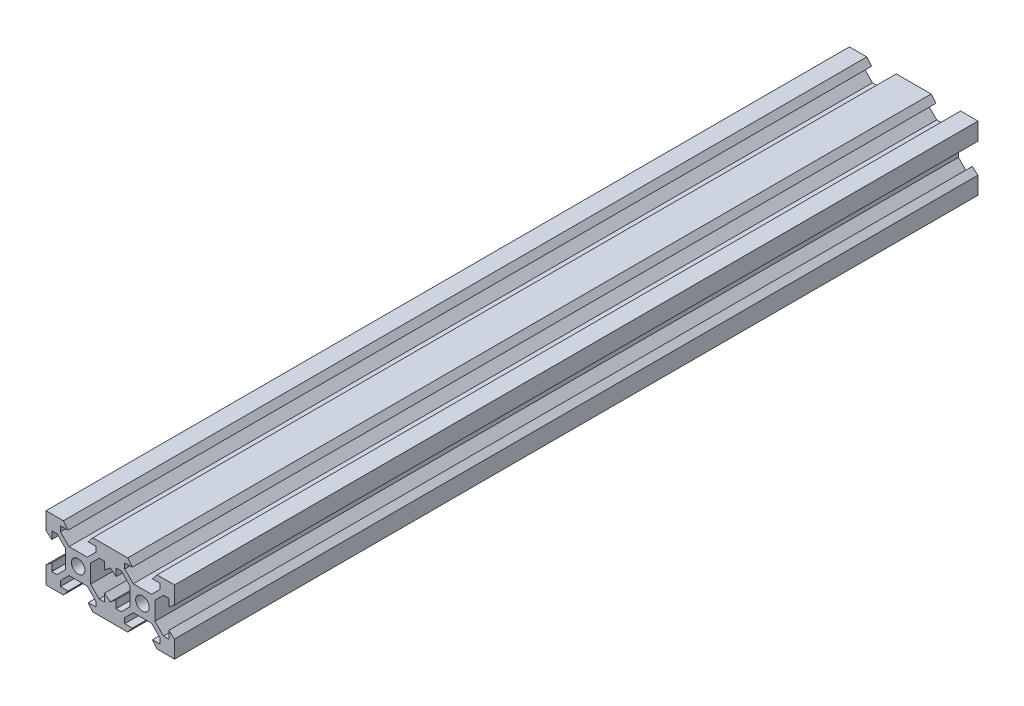
SolidWorks part; units mm, degrees
ref_plane "Front Plane" through (0, 0, 0) normal (0, 0, 1) x (1, 0, 0)
ref_plane "Top Plane" through (0, 0, 0) normal (0, 1, 0) x (1, 0, 0)
ref_plane "Right Plane" through (0, 0, 0) normal (1, 0, 0) x (0, 0, -1)
sketch "Sketch2" plane through (0, 0, 0) normal (0, 0, 1) x (1, 0, 0)
  line L0 (-5.5, 8.2) -> (-5.5, 6.5607)
  line L3 (-10, 10) -> (-4.58, 10)
  line L6 (-10, 10) -> (0, 0)
  line L9 (0, 0) -> (0, 10) construction
  line L16 (-2.8393, 3.9) -> (0, 3.9)
  line L20 (-5.5, 6.5607) -> (-2.8393, 3.9)
  line L21 (-5.5, 8.2) -> (-3.125, 8.2)
  line L22 (-3.125, 8.2) -> (-4.58, 10)
  line L23 (-4.58, 10) -> (-10, 10)
  line L24 (-2.8393, 3.9) -> (0, 3.9)
  line L25 (0, 3.9) -> (0, 2.1)
  line L26 (-3.9, 0) -> (-2.1, 0)
  line L27 (-3.125, 8.2) -> (-5.5, 8.2)
  line L28 (-4.58, 10) -> (-10, 10)
  line L29 (-3.125, 8.2) -> (-5.5, 8.2)
  line L30 (-3.9, 2.8393) -> (-3.9, 0)
  line L32 (-6.5607, 5.5) -> (-3.9, 2.8393)
  line L33 (-8.2, 5.5) -> (-6.5607, 5.5)
  line L34 (-8.2, 5.5) -> (-8.2, 3.125)
  line L35 (-8.2, 3.125) -> (-10, 4.58)
  line L36 (-10, 10) -> (-10, 4.58)
  line L37 (10, 10) -> (10, 4.58)
  line L38 (10, 10) -> (4.58, 10)
  line L39 (3.125, 8.2) -> (4.58, 10)
  line L40 (5.5, 8.2) -> (3.125, 8.2)
  line L41 (5.5, 8.2) -> (5.5, 6.5607)
  line L42 (5.5, 6.5607) -> (2.8393, 3.9)
  line L43 (2.8393, 3.9) -> (0, 3.9)
  line L44 (3.9, 2.8393) -> (3.9, 0)
  line L45 (6.5607, 5.5) -> (3.9, 2.8393)
  line L46 (8.2, 5.5) -> (6.5607, 5.5)
  line L47 (8.2, 5.5) -> (8.2, 3.125)
  line L48 (8.2, 3.125) -> (10, 4.58)
  line L49 (10, -10) -> (4.58, -10)
  line L50 (10, -10) -> (10, -4.58)
  line L51 (8.2, -3.125) -> (10, -4.58)
  line L52 (8.2, -5.5) -> (8.2, -3.125)
  line L53 (8.2, -5.5) -> (6.5607, -5.5)
  line L54 (6.5607, -5.5) -> (3.9, -2.8393)
  line L55 (3.9, -2.8393) -> (3.9, 0)
  line L56 (2.8393, -3.9) -> (0, -3.9)
  line L57 (5.5, -6.5607) -> (2.8393, -3.9)
  line L58 (5.5, -8.2) -> (5.5, -6.5607)
  line L59 (5.5, -8.2) -> (3.125, -8.2)
  line L60 (3.125, -8.2) -> (4.58, -10)
  line L61 (-10, -10) -> (-10, -4.58)
  line L62 (-10, -10) -> (-4.58, -10)
  line L63 (-3.125, -8.2) -> (-4.58, -10)
  line L64 (-5.5, -8.2) -> (-3.125, -8.2)
  line L65 (-5.5, -8.2) -> (-5.5, -6.5607)
  line L66 (-5.5, -6.5607) -> (-2.8393, -3.9)
  line L67 (-2.8393, -3.9) -> (0, -3.9)
  line L68 (-3.9, -2.8393) -> (-3.9, 0)
  line L69 (-6.5607, -5.5) -> (-3.9, -2.8393)
  line L70 (-8.2, -5.5) -> (-6.5607, -5.5)
  line L71 (-8.2, -5.5) -> (-8.2, -3.125)
  line L72 (-8.2, -3.125) -> (-10, -4.58)
  circle A0 centre (0, 0) radius 2.1
  circle A1 centre (0, 0) radius 2.1
  circle A2 centre (0, 0) radius 2.1
  circle A3 centre (0, 0) radius 2.1
  point P64 (0, 0)
  dimension "D1" = 4.2
  dimension "D2" = 6.1
  dimension "D3" = 10
  dimension "D4" = 0.75
  dimension "D5" = 1.8
  dimension "D6" = 5.5
  dimension "D7" = 3.125
  dimension "D8" = 4.58
  dimension "D9" = 10
  dimension "D10" = 10
  dimension "D11" = 4
extrude "Boss-Extrude1" add sketch "Sketch2" along normal blind 250 contours A0 L26 L68 L69 L70 L71 L72 L61 L62 L63 L64 L65 L66 L67 L56 L57 L58 L59 L60 L49 L50 L51 L52 L53 L54 L55 L44 L45 L46 L47 L48 L37 L38 L39 L40 L41 L42 L43 L25 | A0 L6 L36 L35 L34 L33 L32 L30 L26 | A0 L25 L16 L20 L0 L21 L22 L3 L6
mirror "Mirror1" about plane through (10, 0, 250) normal (1, 0, 0) of "Boss-Extrude1"
